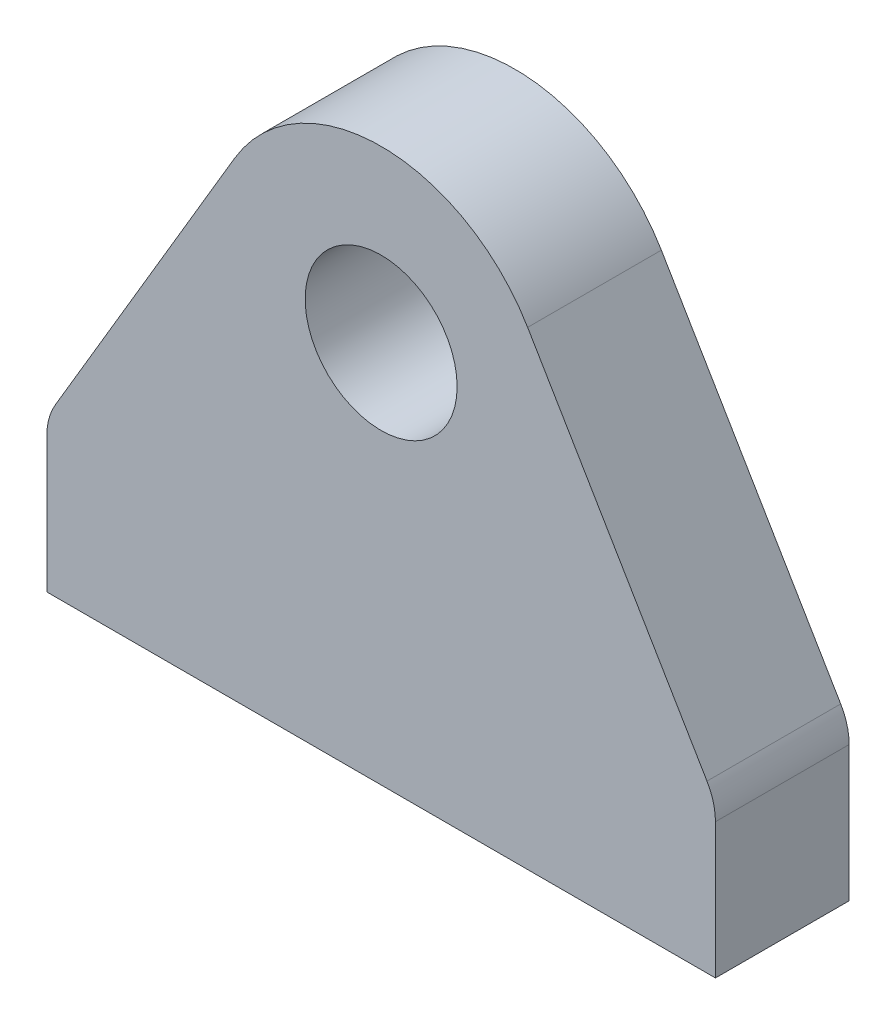
SolidWorks part; units mm, degrees
material "Plain Carbon Steel"
ref_plane "Front Plane" through (0, 0, 0) normal (0, 0, 1) x (1, 0, 0)
ref_plane "Top Plane" through (0, 0, 0) normal (0, 1, 0) x (1, 0, 0)
ref_plane "Right Plane" through (0, 0, 0) normal (1, 0, 0) x (0, 0, -1)
sketch "Sketch1" plane through (0, 0, 0) normal (0, 0, 1) x (1, 0, 0)
  line L0 (-55, 0) -> (55, 0)
  line L1 (55, 0) -> (55, 25)
  line L2 (55, 25) -> (-55, 25) construction
  line L3 (-55, 0) -> (-55, 25)
  line L4 (0, 25) -> (0, 219.9692) construction
  line L5 (-28, 25) -> (-28, 63)
  line L6 (28, 25) -> (28, 63)
  line L7 (-55, 25) -> (-28, 25)
  line L8 (28, 25) -> (55, 25)
  arc A0 (-28, 63) -> (28, 63) centre (0, 63) cw
  circle A1 centre (0, 63) radius 12.5
  dimension "D3" = 28
  dimension "D4" = 25
  dimension "D1" = 25
  dimension "D2" = 110
  dimension "D5" = 38
extrude "Boss-Extrude1" add sketch "Sketch1" along normal mid plane 22
sketch "Sketch2" plane through (0, 0, 11) normal (0, 0, 1) x (1, 0, 0)
  line L0 (-55, 25) -> (-24.1014, 77.2521)
  line L1 (55, 25) -> (24.1014, 77.2521)
  line L2 (55, 25) -> (28, 25) construction
  line L3 (28, 25) -> (28, 63) construction
  line L4 (-28, 63) -> (-28, 25) construction
  line L5 (-28, 25) -> (-55, 25) construction
  line L6 (55, 25) -> (28, 25)
  line L7 (28, 25) -> (28, 63)
  line L8 (-28, 63) -> (-28, 25)
  line L9 (-28, 25) -> (-55, 25)
  arc A0 (28, 63) -> (-28, 63) centre (0, 63) ccw construction
  arc A1 (28, 63) -> (24.1014, 77.2521) centre (0, 63) ccw
  arc A2 (-24.1014, 77.2521) -> (-28, 63) centre (0, 63) ccw
extrude "Boss-Extrude2" add sketch "Sketch2" against normal up to surface (22 mm away) up to face at (0, 31.75, -11)
fillet "Fillet1" radius 10 2 edges at (55, 25, 0) (-55, 25, 0)
